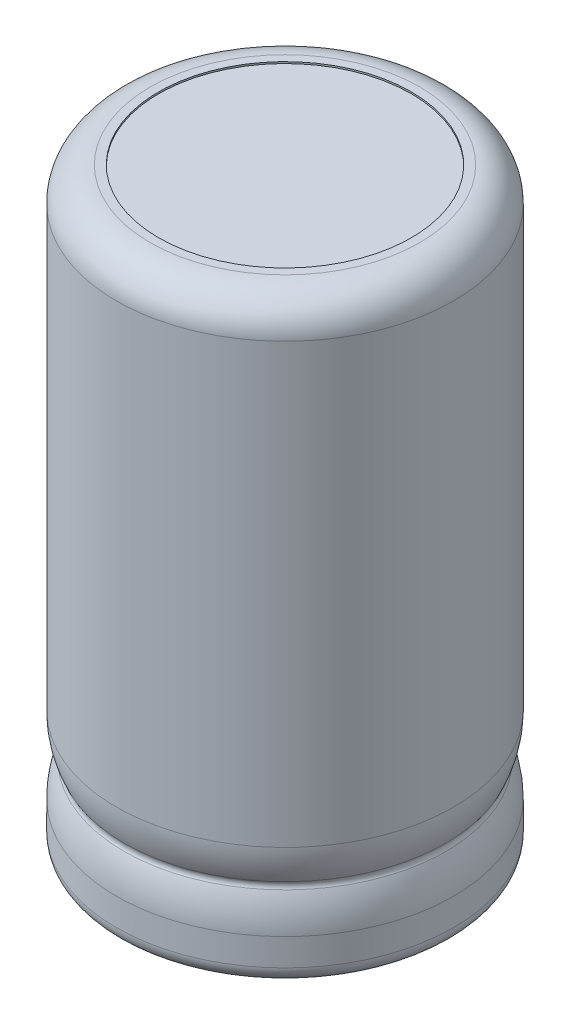
SolidWorks part; units mm, degrees
ref_plane "Front Plane" through (0, 0, 0) normal (0, 0, 1) x (1, 0, 0)
ref_plane "Top Plane" through (0, 0, 0) normal (0, 1, 0) x (1, 0, 0)
ref_plane "Right Plane" through (0, 0, 0) normal (1, 0, 0) x (0, 0, -1)
sketch "Sketch1" plane through (0, 0, 0) normal (0, 1, 0) x (1, 0, 0)
  circle A0 centre (0, 0) radius 0.5
  dimension "D1" = 1
extrude "Base-Extrude" add sketch "Sketch1" against normal blind 3
sketch "Sketch2" plane through (0, 0, 0) normal (0, 1, 0) x (1, 0, 0)
  line L0 (0, 0) -> (-7.1077, 0) construction
  circle A0 centre (-5.08, 0) radius 7.5
  dimension "D1" = 15
  dimension "D2" = 2.42
extrude "Boss-Extrude1" add sketch "Sketch2" along normal blind 0.6908
sketch "Sketch3" plane through (0, 0, 0) normal (0, -1, 0) x (1, 0, 0)
  line L0 (-10.16, 0) -> (4.8337, 0) construction
  circle A0 centre (-10.16, 0) radius 0.5
  circle A1 centre (0, 0) radius 0.5 construction
  dimension "D1" = 9.66
extrude "Boss-Extrude2" add sketch "Sketch3" along normal blind 3
sketch "Sketch4" plane through (0, 0, 0) normal (0, -1, 0) x (1, 0, 0)
  circle A0 centre (-5.08, 0) radius 7.5 construction
  circle A2 centre (-5.08, 0) radius 10
  dimension "D2" = 20
extrude "Boss-Extrude3" add sketch "Sketch4" against normal blind 35.2
sketch "Sketch5" plane through (0, 0, 0) normal (0, -1, 0) x (1, 0, 0)
  circle A0 centre (-5.08, 0) radius 7.5
  circle A1 centre (-5.08, 0) radius 10 construction
  circle A2 centre (0, 0) radius 0.5 construction
  circle A3 centre (-10.16, 0) radius 0.5 construction
  circle A4 centre (0, 0) radius 0.5
  circle A5 centre (-10.16, 0) radius 0.5
  dimension "D1" = 15
extrude "Cut-Extrude1" cut sketch "Sketch5" against normal blind 0.1
fillet "Fillet1" radius 2 1 edges at (-5.08, 35.2, -10)
fillet "Fillet2" radius 1 1 edges at (-5.08, 0, -10)
sketch "Sketch6" plane through (0, 0, 0) normal (0, 0, 1) x (1, 0, 0)
  line L0 (4.465, 18.9297) -> (4.465, 2.0888) construction
  line L1 (-1.4812, 5.11) -> (18.0907, 5.11) construction
  line L2 (-0.7226, 4.69) -> (26.4353, 4.69) construction
  line L3 (-5.08, 0) -> (-5.08, 22.2676) construction
  line L4 (-12.58, 0) -> (2.42, 0) construction
  line L5 (-5.08, 33.2) -> (-5.08, 1) construction
  line L6 (-1.4812, 7.19) -> (20.6699, 7.19) construction
  line L7 (-2.3915, 2.61) -> (20.6699, 2.61) construction
  line L8 (4.92, 1) -> (4.92, 33.2) construction
  line L9 (4.92, 7.19) -> (5.42, 7.19)
  line L10 (5.42, 7.19) -> (5.42, 2.61)
  line L11 (5.42, 2.61) -> (4.92, 2.61)
  arc A0 (4.92, 7.19) -> (4.465, 5.11) centre (-0.0618, 7.19) cw
  arc A1 (4.465, 5.11) -> (4.465, 4.69) centre (4.765, 4.9) ccw
  arc A2 (4.465, 4.69) -> (4.92, 2.61) centre (-0.0618, 2.61) cw
  dimension "D1" = 0.42
  dimension "D2" = 4.69
  dimension "D3" = 9.545
  dimension "D4" = 4.58
  dimension "D5" = 2.61
  dimension "D6" = 0.3
  dimension "D7" = 0.5
revolve "Cut-Revolve1" cut sketch "Sketch6" angle 360 about L3
sketch "Sketch7" plane through (0, 35.2, 0) normal (0, 1, 0) x (-1, 0, 0)
  circle A0 centre (5.08, 0) radius 7.5
  circle A1 centre (5.08, 0) radius 8 construction
  dimension "D1" = 15
extrude "Cut-Extrude2" cut sketch "Sketch7" against normal blind 0.1
ref_plane "Board Plane" through (0, -0.3, 0) normal (0, 1, 0) x (-1, 0, 0)
sketch "Component_Outline" plane through (0, -0.3, 0) normal (0, 1, 0) x (-1, 0, 0)
  circle A0 centre (5.08, 0) radius 10
  circle A1 centre (5.08, 0) radius 10 construction
  point P4 (0, 0)
